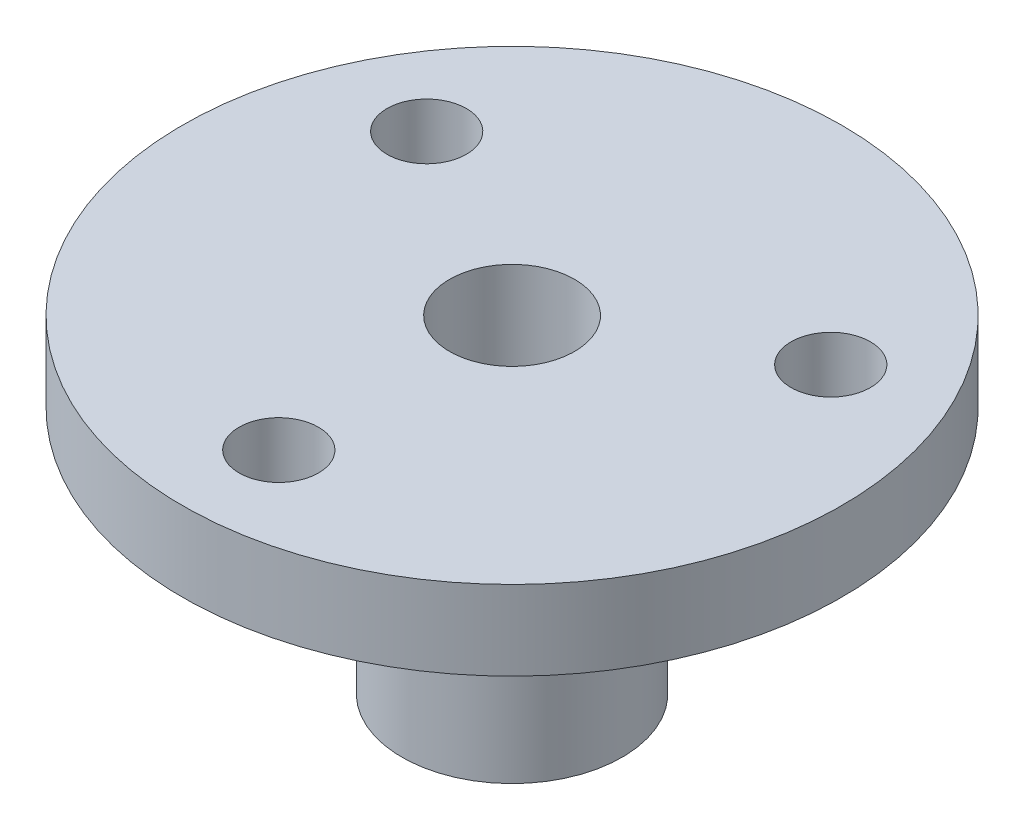
SolidWorks part; units mm, degrees
material "ABS"
ref_plane "Plan de face" through (0, 0, 0) normal (0, 0, 1) x (1, 0, 0)
ref_plane "Plan de dessus" through (0, 0, 0) normal (0, 1, 0) x (1, 0, 0)
ref_plane "Plan de droite" through (0, 0, 0) normal (1, 0, 0) x (0, 0, -1)
sketch "Esquisse1" plane through (0, 0, 0) normal (0, 0, 1) x (1, 0, 0)
  line L0 (0, 0) -> (0, 16.5) construction
  line L1 (16.6, 16.5) -> (3.15, 16.5)
  line L2 (3.15, 16.5) -> (3.15, 0)
  line L3 (3.15, 0) -> (5.55, 0)
  line L4 (5.55, 0) -> (5.55, 10)
  line L5 (8.05, 12.5) -> (16.6, 12.5)
  line L6 (16.6, 12.5) -> (16.6, 16.5)
  arc A0 (8.05, 12.5) -> (5.55, 10) centre (8.05, 10) ccw
  dimension "D6" = 2.5
  dimension "D1" = 4
  dimension "D2" = 16.6
  dimension "D3" = 11.1
  dimension "D4" = 6.3
  dimension "D5" = 16.5
revolve "Révolution1" add sketch "Esquisse1" angle 360 about L0
sketch "Esquisse2" plane through (0, 12.5, 0) normal (0, -1, 0) x (1, 0, 0)
  circle A0 centre (0, 11.75) radius 2
  circle A1 centre (0, 0) radius 16.6 construction
  circle A2 centre (10.1758, -5.875) radius 2
  circle A3 centre (-10.1758, -5.875) radius 2
  point P12 (0, 0)
  dimension "D2" = 4
  dimension "D1" = 11.75
  dimension "D3" = 3
extrude "Enlèv. mat.-Extru.1" cut sketch "Esquisse2" against normal through all
